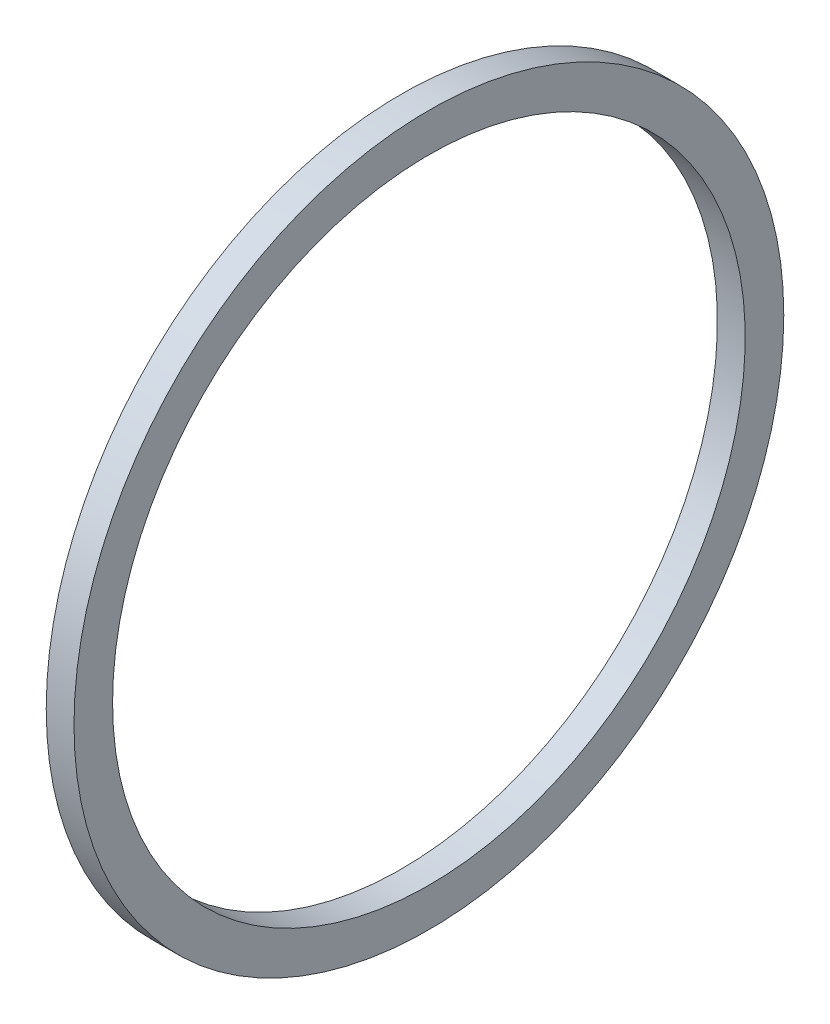
SolidWorks part; units mm, degrees
ref_plane "Front Plane" through (0, 0, 0) normal (0, 0, 1) x (1, 0, 0)
ref_plane "Top Plane" through (0, 0, 0) normal (0, 1, 0) x (1, 0, 0)
ref_plane "Right Plane" through (0, 0, 0) normal (1, 0, 0) x (0, 0, -1)
sketch "Sketch1" plane through (0, 0, 0) normal (0, 0, 1) x (1, 0, 0)
  line L0 (0, 108.75) -> (0, 0) construction
  line L1 (0, 0) -> (81.6598, 0) construction
  line L3 (-4.5, 102.5) -> (4.5, 102.5)
  line L4 (-4.5, 102.5) -> (-4.5, 115)
  line L5 (-4.5, 115) -> (4.5, 115)
  line L6 (4.5, 102.5) -> (4.5, 115)
  line L7 (-4.5, 102.5) -> (4.5, 115) construction
  line L8 (-4.5, 115) -> (4.5, 102.5) construction
  dimension "D1" = 102.5
  dimension "D2" = 115
  dimension "D3" = 9
revolve "Revolve1" add sketch "Sketch1" angle 360 about L1
